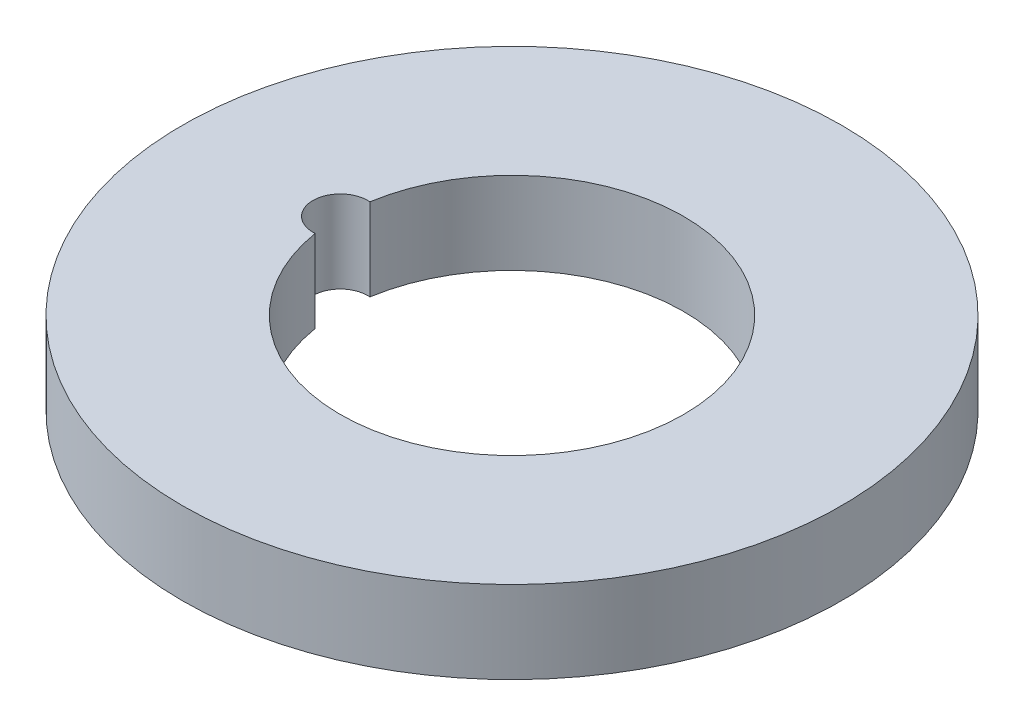
SolidWorks part; units mm, degrees
ref_plane "Ön Düzlem" through (0, 0, 0) normal (0, 0, 1) x (1, 0, 0)
ref_plane "Üst Düzlem" through (0, 0, 0) normal (0, 1, 0) x (1, 0, 0)
ref_plane "Sağ Düzlem" through (0, 0, 0) normal (1, 0, 0) x (0, 0, -1)
sketch "Çizim1" plane through (0, 0, 0) normal (0, 1, 0) x (1, 0, 0)
  arc A0 (-6.17, -0.9968) -> (-6.17, 0.9968) centre (0, 0) ccw
  circle A1 centre (0, 0) radius 12
  arc A2 (-6.17, 0.9968) -> (-6.17, -0.9968) centre (-6.25, 0) ccw
  dimension "D1" = 24
  dimension "D2" = 12.5
  dimension "D3" = 2
extrude "Yükseklik-Ekstrüzyon1" add sketch "Çizim1" along normal blind 3
